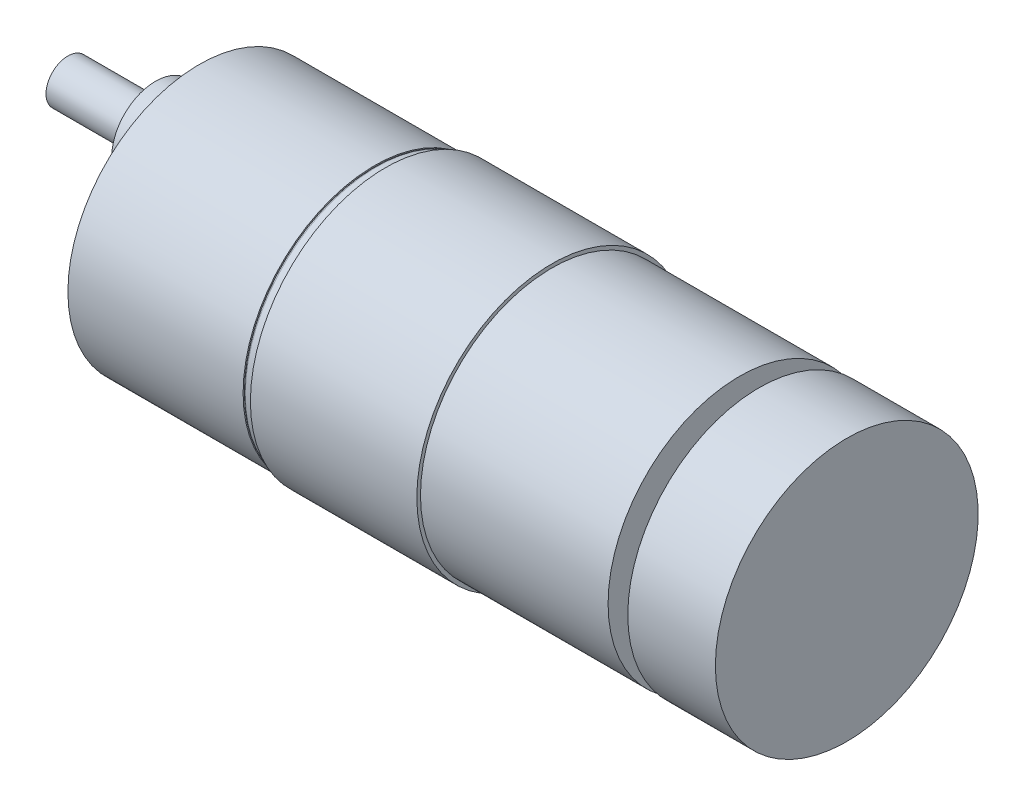
SolidWorks part; units mm, degrees
ref_plane "前视基准面" through (0, 0, 0) normal (0, 0, 1) x (1, 0, 0)
ref_plane "上视基准面" through (0, 0, 0) normal (0, 1, 0) x (1, 0, 0)
ref_plane "右视基准面" through (0, 0, 0) normal (1, 0, 0) x (0, 0, -1)
sketch "草图5" plane through (0, 0, 0) normal (0, 0, 1) x (1, 0, 0)
  line L0 (-65.6791, 0) -> (88.7, 0) construction
  line L1 (0, 0) -> (0, 18)
  line L2 (0, 18) -> (24, 18)
  line L3 (24, 18) -> (24, 17.7)
  line L4 (101.5883, 0) -> (120.9878, 0) construction
  line L5 (24.3, 18) -> (25.5, 18)
  line L6 (25.5, 18) -> (25.5, 18.5)
  line L7 (25.5, 18.5) -> (48.3, 18.5)
  line L8 (48.3, 18.5) -> (48.3, 18)
  line L9 (48.3, 18) -> (74, 18)
  line L10 (74, 18) -> (74, 6)
  line L11 (74, 6) -> (76.7, 6)
  line L12 (76.7, 6) -> (76.7, 18)
  line L13 (76.7, 18) -> (88.7, 18)
  line L14 (88.7, 18) -> (88.7, 0)
  line L17 (0, 0) -> (88.7, 0)
  arc A0 (24, 17.7) -> (24.3, 18) centre (24.3, 17.7) cw
  dimension "D3" = 0.3
  dimension "D1" = 24
  dimension "D2" = 18
  dimension "D4" = 1.2
  dimension "D5" = 0.5
  dimension "D6" = 22.8
  dimension "D7" = 50
  dimension "D8" = 6
  dimension "D9" = 18
  dimension "D10" = 12
  dimension "D11" = 2.7
revolve "旋转1" add sketch "草图5" angle 360 about L0
sketch "草图6" plane through (0, 0, 0) normal (-1, 0, 0) x (0, 0, 1)
  circle A0 centre (0, 7) radius 6
  point P0 (0, 7)
  dimension "D2" = 12
  dimension "D1" = 7
extrude "凸台-拉伸3" add sketch "草图6" along normal blind 6
sketch "草图7" plane through (-6, 0, 0) normal (-1, 0, 0) x (0, 0, 1)
  circle A0 centre (0, 7) radius 3
  dimension "D1" = 6
extrude "凸台-拉伸4" add sketch "草图7" along normal blind 12
sketch "草图8" plane through (0, 0, 0) normal (-1, 0, 0) x (0, 0, 1)
  line L0 (0, 0) -> (25.0064, 0) construction
  circle A0 centre (15.5, 0) radius 1.5
  circle A1 centre (7.75, -13.4234) radius 1.5
  circle A2 centre (-7.75, -13.4234) radius 1.5
  circle A3 centre (-15.5, 0) radius 1.5
  circle A4 centre (-7.75, 13.4234) radius 1.5
  circle A5 centre (7.75, 13.4234) radius 1.5
  point P18 (0, 0)
  dimension "D2" = 3
  dimension "D1" = 15.5
  dimension "D3" = 6
extrude "切除-拉伸22" cut sketch "草图8" against normal blind 12
